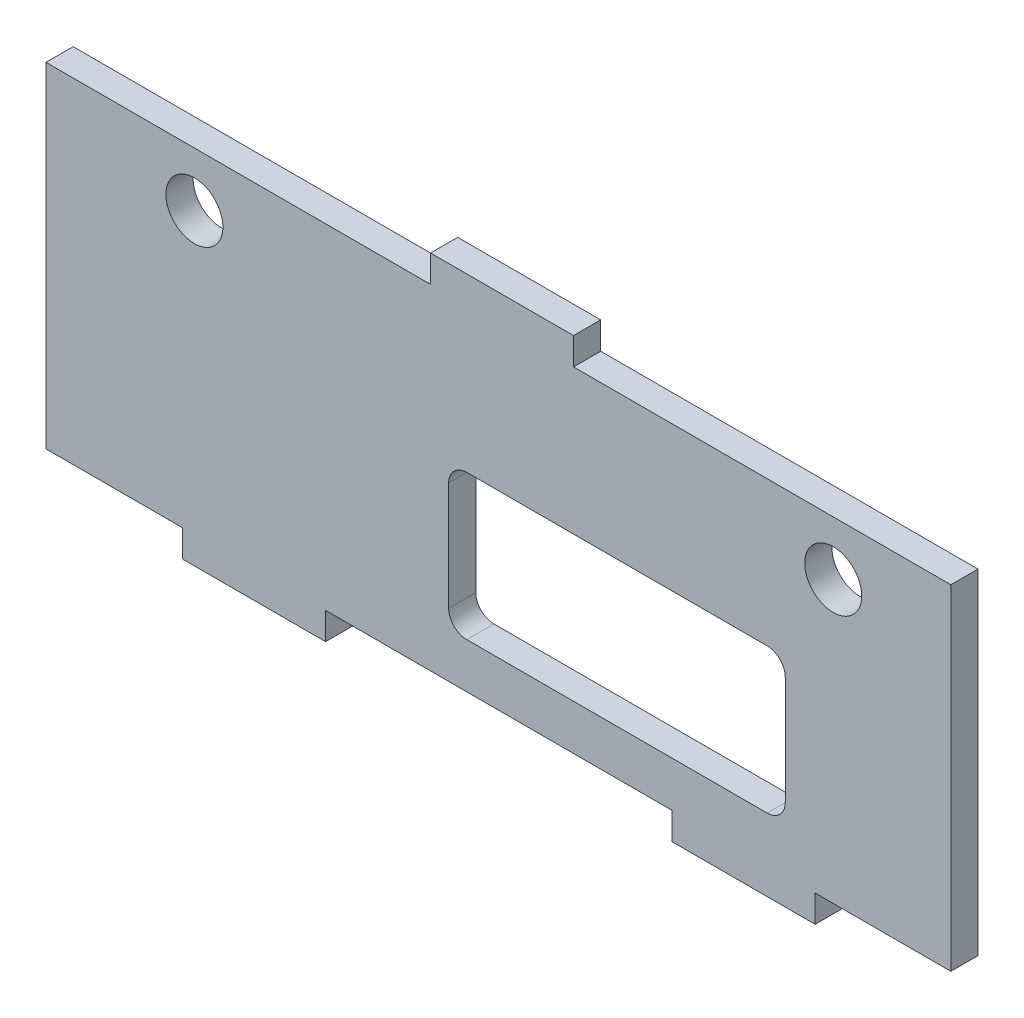
SolidWorks part; units mm, degrees
ref_plane "Alzado" through (0, 0, 0) normal (0, 0, 1) x (1, 0, 0)
ref_plane "Planta" through (0, 0, 0) normal (0, 1, 0) x (1, 0, 0)
ref_plane "Vista lateral" through (0, 0, 0) normal (1, 0, 0) x (0, 0, -1)
sketch "Croquis1" plane through (0, 0, 0) normal (0, 0, 1) x (1, 0, 0)
  line L1 (-50, 21.5) -> (50, 21.5)
  line L2 (-50, 21.5) -> (-50, -21.5)
  line L3 (-50, -21.5) -> (50, -21.5)
  line L4 (50, 21.5) -> (50, -21.5)
  line L5 (-50, 21.5) -> (50, -21.5) construction
  line L6 (-50, -21.5) -> (50, 21.5) construction
  line L7 (50, 21.5) -> (8.3, 21.5)
  line L8 (50, 21.5) -> (50, 18.5)
  line L9 (50, 18.5) -> (8.3, 18.5)
  line L10 (8.3, 21.5) -> (8.3, 18.5)
  line L11 (-50, 21.5) -> (-7.5, 21.5)
  line L12 (-50, 21.5) -> (-50, 18.5)
  line L13 (-50, 18.5) -> (-7.5, 18.5)
  line L14 (-7.5, 21.5) -> (-7.5, 18.5)
  line L15 (-3.5, 2.5) -> (29.7, 2.5)
  line L16 (-5.5, 0.5) -> (-5.5, -11.5)
  line L17 (-3.5, -13.5) -> (29.7, -13.5)
  line L18 (31.7, 0.5) -> (31.7, -11.5)
  line L19 (-50, -21.5) -> (-34.9, -21.5)
  line L20 (-50, -21.5) -> (-50, -18.5)
  line L21 (-50, -18.5) -> (-34.9, -18.5)
  line L22 (-34.9, -21.5) -> (-34.9, -18.5)
  line L23 (-19.1, -21.5) -> (19.2, -21.5)
  line L24 (-19.1, -21.5) -> (-19.1, -18.5)
  line L25 (-19.1, -18.5) -> (19.2, -18.5)
  line L26 (19.2, -21.5) -> (19.2, -18.5)
  line L27 (50, -21.5) -> (35, -21.5)
  line L28 (50, -21.5) -> (50, -18.5)
  line L29 (50, -18.5) -> (35, -18.5)
  line L30 (35, -21.5) -> (35, -18.5)
  circle A0 centre (37, 12.5) radius 3.15
  circle A1 centre (-33.6, 12.5) radius 3.15
  arc A2 (31.7, -11.5) -> (29.7, -13.5) centre (29.7, -11.5) cw
  arc A3 (-5.5, -11.5) -> (-3.5, -13.5) centre (-3.5, -11.5) ccw
  arc A4 (31.7, 0.5) -> (29.7, 2.5) centre (29.7, 0.5) ccw
  arc A5 (-3.5, 2.5) -> (-5.5, 0.5) centre (-3.5, 0.5) ccw
  point P0 (0, 0)
  point P30 (-34.9, -20)
  point P33 (31.7, -13.5)
  point P36 (-5.5, -13.5)
  point P41 (-5.5, 2.5)
  dimension "D3" = 6.3
  dimension "D22" = 2
  dimension "D1" = 100
  dimension "D2" = 43
  dimension "D5" = 3
  dimension "D6" = 15.8
  dimension "D7" = 41.7
  dimension "D8" = 3
  dimension "D9" = 37
  dimension "D10" = 37.2
  dimension "D11" = 16
  dimension "D12" = 15
  dimension "D13" = 15.8
  dimension "D14" = 38.3
  dimension "D15" = 15.8
  dimension "D16" = 15.1
  dimension "D17" = 18.3
  dimension "D18" = 16
  dimension "D19" = 13
  dimension "D20" = 6
  dimension "D21" = 70.6
  dimension "D4" = 2
extrude "Saliente-Extruir1" add sketch "Croquis1" along normal blind 3 contours L3 L30 L29 L4 L9 L10 L1 L14 L13 L2 L21 L22 L24 L25 L26 A5 L15 A4 L18 A2 L17 A3 L16 A1 A0
